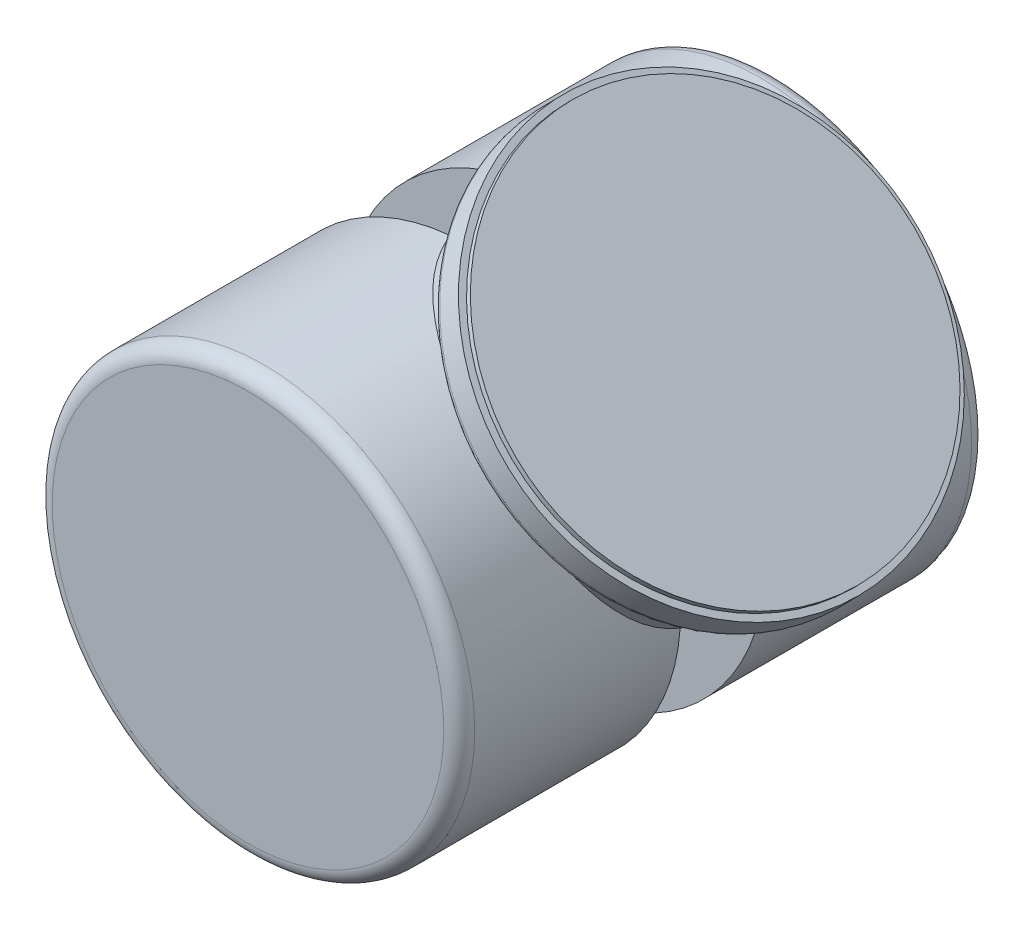
SolidWorks part; units mm, degrees
ref_plane "Front Plane" through (0, 0, 0) normal (0, 0, 1) x (1, 0, 0)
ref_plane "Top Plane" through (0, 0, 0) normal (0, 1, 0) x (1, 0, 0)
ref_plane "Right Plane" through (0, 0, 0) normal (1, 0, 0) x (0, 0, -1)
sketch "Sketch1" plane through (0, 0, 0) normal (1, 0, 0) x (0, 0, -1)
  line L0 (0, 304.8) -> (0, -304.8)
  dimension "D1" = 609.6
surface "Surface-Extrude1" [suppressed] sketch "Sketch1" parameters "D1"=609.6
sketch "Sketch2" plane through (0, 0, 0) normal (0, 0, 1) x (1, 0, 0)
  line L0 (-4.8859, 8.46) -> (97.4994, 113.1249) construction
  circle A0 centre (-4.8859, 8.46) radius 34.7138
extrude "Boss-Extrude1" add sketch "Sketch2" along normal mid plane 86.7319
sketch "Sketch3" plane through (0, 0, 0) normal (0, 0, 1) x (1, 0, 0)
  line L0 (22.6172, -2.9546) -> (39.9919, 15.7567)
  line L1 (41.7868, 15.8232) -> (42.8982, 14.7912)
  line L2 (42.8982, 14.7912) -> (48.0742, 14.7912)
  line L3 (48.982, 15.1731) -> (52.0648, 18.3245)
  line L4 (22.6172, -2.9546) -> (2.857, 16.3753)
  line L5 (-4.8859, 8.46) -> (97.4994, 113.1249) construction
  line L6 (2.857, 16.3753) -> (28.5152, 42.6048)
  line L7 (51.2923, 19.0802) -> (52.0648, 18.3245)
  line L8 (28.5152, 42.6048) -> (51.914, 19.7157)
  line L9 (51.914, 19.7157) -> (51.2923, 19.0802)
  arc A0 (39.9919, 15.7567) -> (41.7868, 15.8232) centre (40.9226, 14.8925) cw
  arc A1 (48.0742, 14.7912) -> (48.982, 15.1731) centre (48.0742, 16.0612) ccw
  dimension "D2" = 1.27
  dimension "D3" = 1.27
  dimension "D1" = 0.889
revolve "Revolve1" add sketch "Sketch3" angle 360 about L6
fillet "Fillet1" radius 2.54 2 edges at (29.8279, 8.46, 43.366) (29.8279, 8.46, -43.366)
sketch "Sketch4" plane through (0, 0, 0) normal (0, 0, 1) x (1, 0, 0)
  circle A0 centre (-4.8859, 8.46) radius 34.7138 construction
  circle A1 centre (-4.8859, 8.46) radius 34.7138
extrude "Cut-Extrude1" cut sketch "Sketch4" against normal mid plane 13.97
scale "Scale1" bodies to scale 111 102 scale about origin uniform scaling yes scale factor 2.102564
